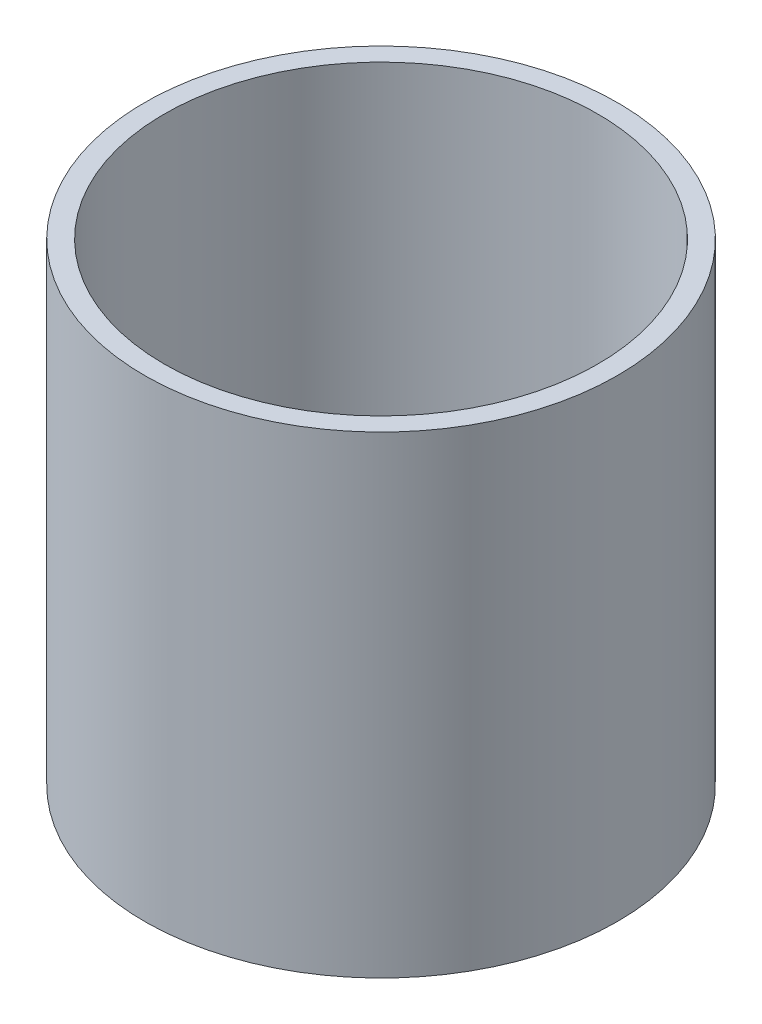
SolidWorks part; units mm, degrees
ref_plane "Спереди" through (0, 0, 0) normal (0, 0, 1) x (1, 0, 0)
ref_plane "Сверху" through (0, 0, 0) normal (0, 1, 0) x (1, 0, 0)
ref_plane "Справа" through (0, 0, 0) normal (1, 0, 0) x (0, 0, -1)
sketch "Эскиз1" plane through (0, 0, 0) normal (0, 1, 0) x (1, 0, 0)
  circle A0 centre (0, 0) radius 55
extrude "Вытянуть-Тонкостенный1" add sketch "Эскиз1" along normal blind 120 thin
